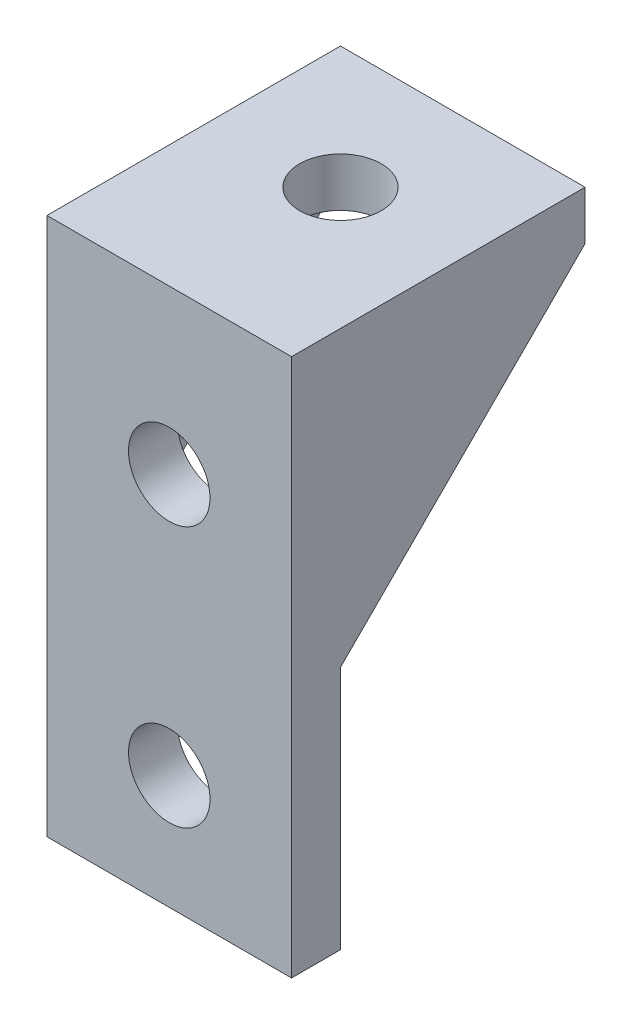
SolidWorks part; units mm, degrees
ref_plane "Front Plane" through (0, 0, 0) normal (0, 0, 1) x (1, 0, 0)
ref_plane "Top Plane" through (0, 0, 0) normal (0, 1, 0) x (1, 0, 0)
ref_plane "Right Plane" through (0, 0, 0) normal (1, 0, 0) x (0, 0, -1)
sketch "Sketch1" plane through (0, 0, 0) normal (0, 0, 1) x (1, 0, 0)
  line L1 (-7.5, -15) -> (7.5, -15)
  line L2 (-7.5, -15) -> (-7.5, 15)
  line L3 (-7.5, 15) -> (7.5, 15)
  line L4 (7.5, -15) -> (7.5, 15)
  line L5 (-7.5, -15) -> (7.5, 15) construction
  line L6 (-7.5, 15) -> (7.5, -15) construction
  circle A0 centre (0, 8) radius 2.5
  circle A1 centre (0, -8) radius 2.5
  point P0 (0, 0)
  dimension "D1" = 5
  dimension "D2" = 16
  dimension "D3" = 8
  dimension "D4" = 15
  dimension "D5" = 30
extrude "Boss-Extrude1" add sketch "Sketch1" along normal blind 3
sketch "Sketch2" plane through (0, 15, 0) normal (0, 1, 0) x (1, 0, 0)
  line L0 (7.5, -3) -> (7.5, 0) construction
  line L1 (-7.5, -3) -> (7.5, -3)
  line L2 (-7.5, -3) -> (-7.5, 15)
  line L3 (-7.5, 15) -> (7.5, 15)
  line L4 (7.5, -3) -> (7.5, 15)
  line L5 (0, 7.5) -> (0, 15) construction
  line L6 (0, 7.5) -> (0, 0) construction
  circle A0 centre (0, 7.5) radius 2.5
  dimension "D2" = 5
  dimension "D1" = 18
extrude "Boss-Extrude2" add sketch "Sketch2" along normal blind 3
sketch "Sketch3" plane through (7.5, 0, 0) normal (1, 0, 0) x (0, 0, -1)
  line L0 (15, 15) -> (0, 0)
  line L1 (0, -15) -> (0, 15) construction
  line L2 (0, 15) -> (15, 15) construction
  line L3 (15, 15) -> (0, 15)
  line L4 (0, 15) -> (0, 0)
  dimension "D1" = 45
extrude "Boss-Extrude3" add sketch "Sketch3" against normal blind 2
mirror "Mirror1" about plane through (0, 0, 0) normal (1, 0, 0) of "Boss-Extrude3"
